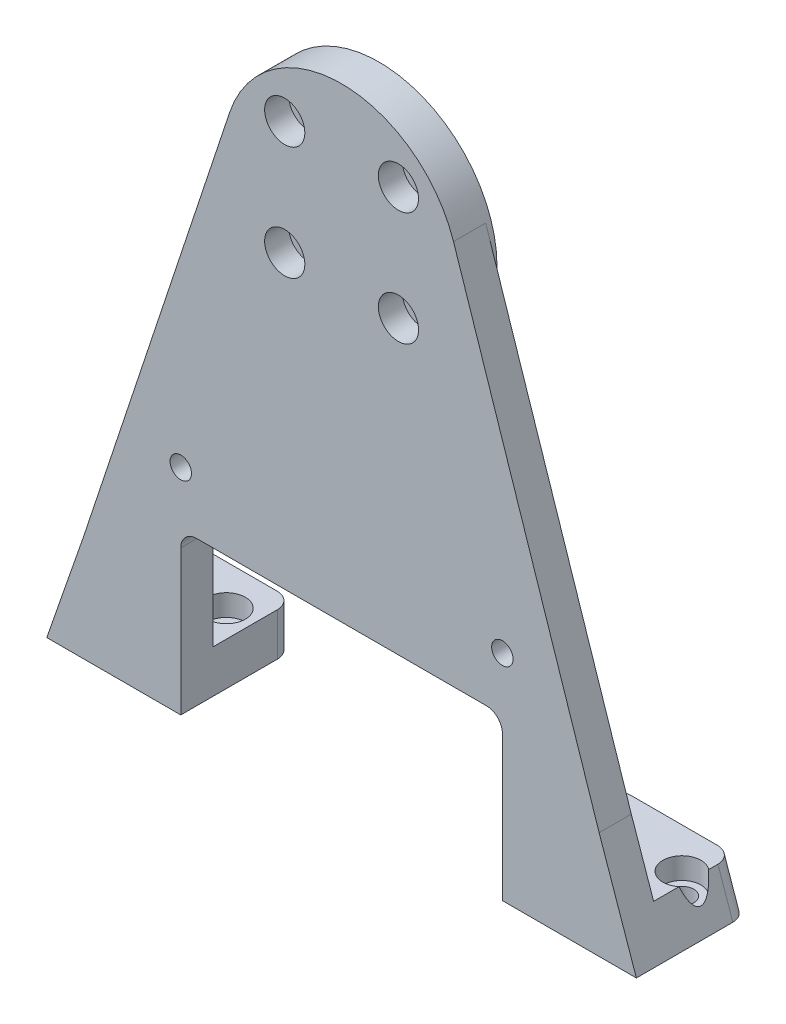
SolidWorks part; units mm, degrees
ref_plane "Front Plane" through (0, 0, 0) normal (0, 0, 1) x (1, 0, 0)
ref_plane "Top Plane" through (0, 0, 0) normal (0, 1, 0) x (1, 0, 0)
ref_plane "Right Plane" through (0, 0, 0) normal (1, 0, 0) x (0, 0, -1)
sketch "Sketch1" plane through (0, 0, 0) normal (0, 0, 1) x (1, 0, 0)
  line L0 (0, 0) -> (0, 33.5533) construction
  line L1 (0, 0) -> (10.6066, 10.6066) construction
  circle A0 centre (0, 0) radius 22
  circle A1 centre (10.6066, 10.6066) radius 2.2
  circle A2 centre (10.6066, -10.6066) radius 2.2
  circle A3 centre (-10.6066, -10.6066) radius 2.2
  circle A4 centre (-10.6066, 10.6066) radius 2.2
  point P14 (0, 0)
  dimension "D1" = 44
  dimension "D3" = 4.4
  dimension "D2" = 15
  dimension "D5" = 45
  dimension "D4" = 4
extrude "Boss-Extrude1" add sketch "Sketch1" along normal blind 1
sketch "Sketch2" plane through (0, 0, 1) normal (0, 0, 1) x (1, 0, 0)
  line L0 (-55, -95) -> (55, -95)
  line L1 (55, -95) -> (48.055, -75)
  line L3 (-48.055, -75) -> (-55, -95)
  line L4 (-48.055, -75) -> (-20.8813, 6.926)
  line L5 (48.055, -75) -> (20.8813, 6.926)
  line L7 (-30, -95) -> (30, -95)
  line L8 (-30, -95) -> (-30, -65)
  line L9 (-30, -65) -> (30, -65)
  line L10 (30, -95) -> (30, -65)
  circle A0 centre (0, 0) radius 22 construction
  circle A1 centre (10.6066, 10.6066) radius 2.2
  circle A2 centre (10.6066, 10.6066) radius 2.2
  circle A3 centre (10.6066, -10.6066) radius 2.2
  circle A4 centre (10.6066, -10.6066) radius 2.2
  circle A5 centre (-10.6066, -10.6066) radius 2.2
  circle A6 centre (-10.6066, -10.6066) radius 2.2
  circle A7 centre (-10.6066, 10.6066) radius 2.2
  circle A8 centre (-10.6066, 10.6066) radius 2.2
  arc A9 (20.8813, 6.926) -> (-20.8813, 6.926) centre (0, 0) ccw
  circle A10 centre (-30, -55) radius 2
  circle A11 centre (30, -55) radius 2
  point P14 (0, -95)
  point P27 (0, -65)
  circle M16 centre (-10.6066, -10.6066) radius 2.2
  circle M17 centre (10.6066, 10.6066) radius 2.2
  circle M18 centre (0, 0) radius 22
  circle M19 centre (10.6066, -10.6066) radius 2.2
  circle M20 centre (-10.6066, 10.6066) radius 2.2
  dimension "D15" = 4
  dimension "D5" = 96.11
  dimension "D6" = 110
  dimension "D7" = 95
  dimension "D8" = 6.945
  dimension "D9" = 20
  dimension "D10" = 30
  dimension "D11" = 60
  dimension "D12" = 60
  dimension "D13" = 30
  dimension "D14" = 10
  dimension "D1" = 0
  dimension "D2" = 0
  dimension "D3" = 0
  dimension "D4" = 0
extrude "Boss-Extrude2" add sketch "Sketch2" along normal blind 6 contours L10 L0 L1 L5 L4 L3 L8 L9 M18 | M18 M17 M19 M20 M16
sketch "Sketch3" plane through (0, -95, 0) normal (0, -1, 0) x (-1, 0, 0)
  line L0 (-30, -7) -> (-30, -1) construction
  line L1 (-55, -1) -> (-30, -1)
  line L2 (-55, -1) -> (-55, 14)
  line L3 (-55, 14) -> (-30, 14)
  line L4 (-30, -1) -> (-30, 14)
  line L5 (0, 0) -> (0, 14.6522) construction
  line L6 (30, -1) -> (30, 14)
  line L7 (55, 14) -> (30, 14)
  line L8 (55, -1) -> (55, 14)
  line L9 (55, -1) -> (30, -1)
  circle A0 centre (-35, 6.5) radius 2.2
  circle A1 centre (-50, 6.5) radius 2.2
  circle A2 centre (50, 6.5) radius 2.2
  circle A3 centre (35, 6.5) radius 2.2
  point P11 (-30, 6.5)
  dimension "D4" = 4.4
  dimension "D1" = 15
  dimension "D2" = 15
  dimension "D3" = 5
extrude "Boss-Extrude3" add sketch "Sketch3" against normal blind 8
sketch "Sketch4" plane through (0, 0, 1) normal (0, 0, 1) x (1, 0, 0)
  line L0 (-55, -95) -> (-52.222, -87)
  line L1 (-52.222, -87) -> (-55, -87)
  line L2 (-55, -87) -> (-55, -95)
  line L3 (55, -95) -> (55, -87)
  line L4 (55, -87) -> (52.222, -87)
  line L5 (52.222, -87) -> (55, -95)
extrude "Cut-Extrude1" cut sketch "Sketch4" against normal through all
sketch "Sketch5" plane through (0, -87, 0) normal (0, 1, 0) x (1, 0, 0)
  circle A0 centre (-50, 6.5) radius 3.55
  circle A1 centre (-35, 6.5) radius 3.55
  circle A2 centre (35, 6.5) radius 3.55
  circle A3 centre (50, 6.5) radius 3.55
  dimension "D1" = 7.1
extrude "Cut-Extrude2" cut sketch "Sketch5" against normal blind 4
fillet "Fillet1" radius 3 6 edges at (-53.611, -91, -14) (-30, -91, -14) (53.611, -91, -14) (30, -91, -14) (-30, -65, 4) (30, -65, 4)
sketch "Sketch6" plane through (0, 0, 7) normal (0, 0, 1) x (1, 0, 0)
  circle A0 centre (-10.6066, 10.6066) radius 3.75
  circle A1 centre (10.6066, 10.6066) radius 3.75
  circle A2 centre (10.6066, -10.6066) radius 3.75
  circle A3 centre (-10.6066, -10.6066) radius 3.75
  dimension "D1" = 7.5
extrude "Cut-Extrude3" cut sketch "Sketch6" against normal blind 4.5
